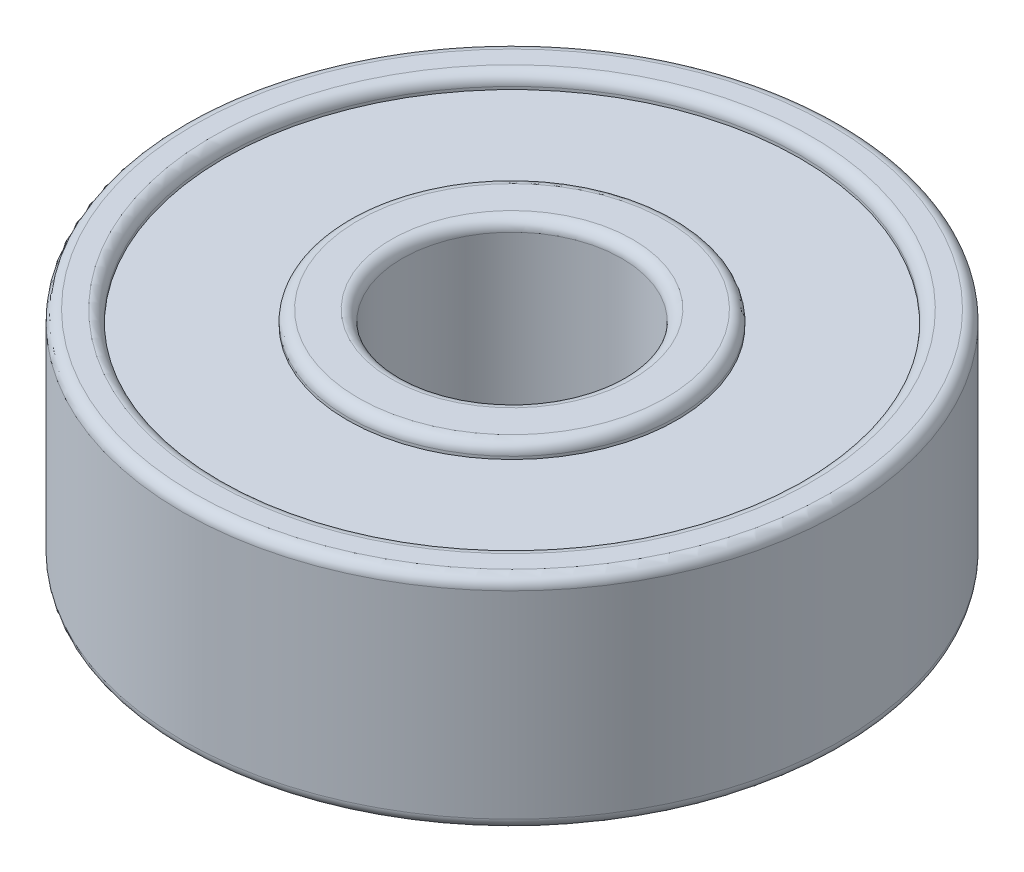
SolidWorks part; units mm, degrees
ref_plane "Front Plane" through (0, 0, 0) normal (0, 0, 1) x (1, 0, 0)
ref_plane "Top Plane" through (0, 0, 0) normal (0, 1, 0) x (1, 0, 0)
ref_plane "Right Plane" through (0, 0, 0) normal (1, 0, 0) x (0, 0, -1)
sketch "Sketch1" plane through (0, 0, 0) normal (0, 1, 0) x (1, 0, 0)
  circle A0 centre (0, 0) radius 6
  circle A1 centre (0, 0) radius 2
extrude "Boss-Extrude1" add sketch "Sketch1" along normal blind 4
sketch "Sketch2" plane through (0, 4, 0) normal (0, 1, 0) x (1, 0, 0)
  circle A0 centre (0, 0) radius 5.25
  circle A1 centre (0, 0) radius 3
extrude "Cut-Extrude1" cut sketch "Sketch2" against normal blind 0.25
sketch "Sketch3" plane through (0, 0, 0) normal (0, -1, 0) x (1, 0, 0)
  circle A0 centre (0, 0) radius 5.25
  circle A1 centre (0, 0) radius 3
extrude "Cut-Extrude2" cut sketch "Sketch3" against normal blind 0.25
fillet "Fillet1" radius 0.2 8 edges at (0, 4, 2) (0, 4, 3) (0, 4, 5.25) (0, 4, 6) (0, 0, 6) (0, 0, 2) (0, 0, -3) (0, 0, -5.25)
